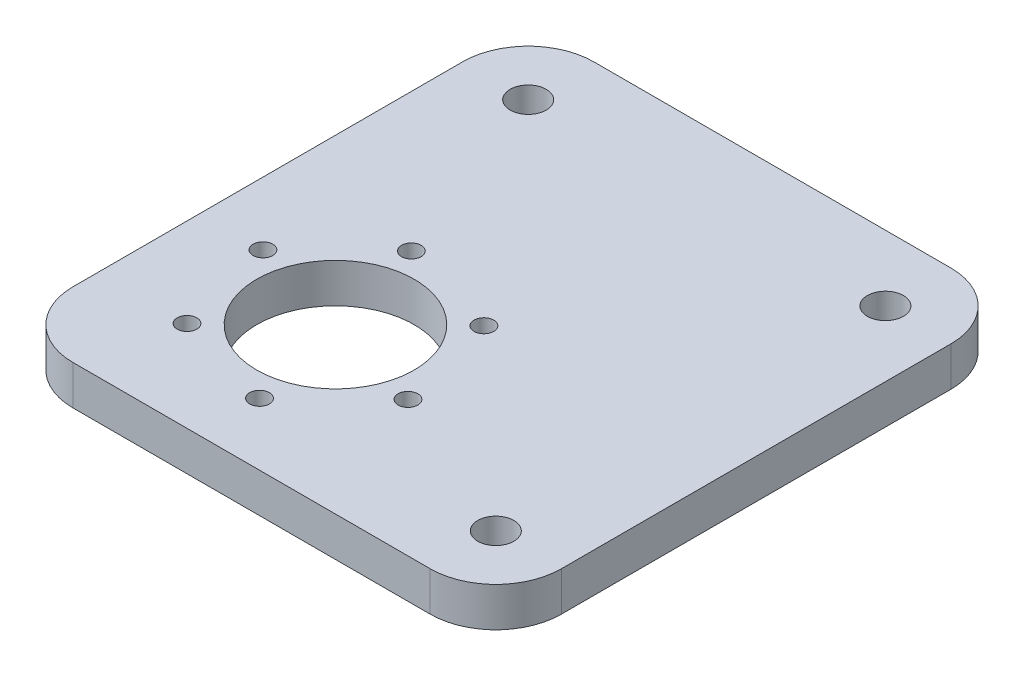
SolidWorks part; units mm, degrees
ref_plane "Front Plane" through (0, 0, 0) normal (0, 0, 1) x (1, 0, 0)
ref_plane "Top Plane" through (0, 0, 0) normal (0, 1, 0) x (1, 0, 0)
ref_plane "Right Plane" through (0, 0, 0) normal (1, 0, 0) x (0, 0, -1)
sketch "Sketch2" plane through (0, 0, 0) normal (0, 1, 0) x (1, 0, 0)
  line L1 (-18.6933, 53.5256) -> (55.7467, 53.5256)
  line L2 (-18.6933, 53.5256) -> (-18.6933, -25.8544)
  line L3 (-18.6933, -25.8544) -> (55.7467, -25.8544)
  line L4 (55.7467, 53.5256) -> (55.7467, -25.8544)
  circle A0 centre (6.3067, -0.8544) radius 12
  dimension "D1" = 24
  dimension "D2" = 74.44
  dimension "D3" = 79.38
extrude "Boss-Extrude1" add sketch "Sketch2" along normal blind 6
sketch "Sketch6" plane through (0, 0, 0) normal (0, -1, 0) x (1, 0, 0)
  line L0 (55.7467, 25.8544) -> (55.7467, -53.5256) construction
  line L1 (55.7467, -53.5256) -> (-18.6933, -53.5256) construction
  line L2 (-18.6933, 25.8544) -> (55.7467, 25.8544) construction
  line L3 (-18.6933, -53.5256) -> (-18.6933, 25.8544) construction
  circle A0 centre (45.7467, 15.8544) radius 2.75
  circle A2 centre (45.7467, -43.5256) radius 2.75
  circle A3 centre (-8.6933, -43.5256) radius 2.75
  dimension "D5" = 5.5
  dimension "D6" = 5.5
  dimension "D7" = 5.5
  dimension "D1" = 10
  dimension "D2" = 10
  dimension "D3" = 10
  dimension "D4" = 10
extrude "Cut-Extrude2" cut sketch "Sketch6" against normal blind 10
sketch "Sketch7" plane through (0, 0, 0) normal (0, -1, 0) x (1, 0, 0)
  circle A0 centre (-5.155, 12.0181) radius 1.25 construction
  circle A1 centre (-5.155, 12.0181) radius 1.25
  circle A2 centre (10.2439, 16.3624) radius 1.25 construction
  circle A3 centre (10.2439, 16.3624) radius 1.25
  circle A4 centre (17.7685, -10.3094) radius 1.25 construction
  circle A5 centre (17.7685, -10.3094) radius 1.25
  circle A6 centre (2.3695, -14.6537) radius 1.25 construction
  circle A7 centre (2.3695, -14.6537) radius 1.25
  circle A8 centre (21.7057, 5.1986) radius 1.25 construction
  circle A9 centre (21.7057, 5.1986) radius 1.25
  circle A10 centre (-9.0922, -3.4899) radius 1.25 construction
  circle A11 centre (-9.0922, -3.4899) radius 1.25
sketch "Sketch8" plane through (0, 0, 0) normal (0, -1, 0) x (1, 0, 0)
  circle A0 centre (21.7057, 5.1986) radius 1.5
  circle A1 centre (17.7685, -10.3094) radius 1.5
  circle A2 centre (2.3695, -14.6537) radius 1.5
  circle A3 centre (-9.0922, -3.4899) radius 1.5
  circle A4 centre (-5.155, 12.0181) radius 1.5
  circle A5 centre (10.2439, 16.3624) radius 1.5
  dimension "D1" = 3
  dimension "D2" = 3
  dimension "D3" = 3
  dimension "D4" = 3
  dimension "D5" = 3
  dimension "D6" = 3
extrude "Cut-Extrude4" cut sketch "Sketch8" against normal through all
fillet "Fillet1" radius 10 4 edges at (55.7467, 3, -53.5256) (-18.6933, 3, -53.5256) (-18.6933, 3, 25.8544) (55.7467, 3, 25.8544)
